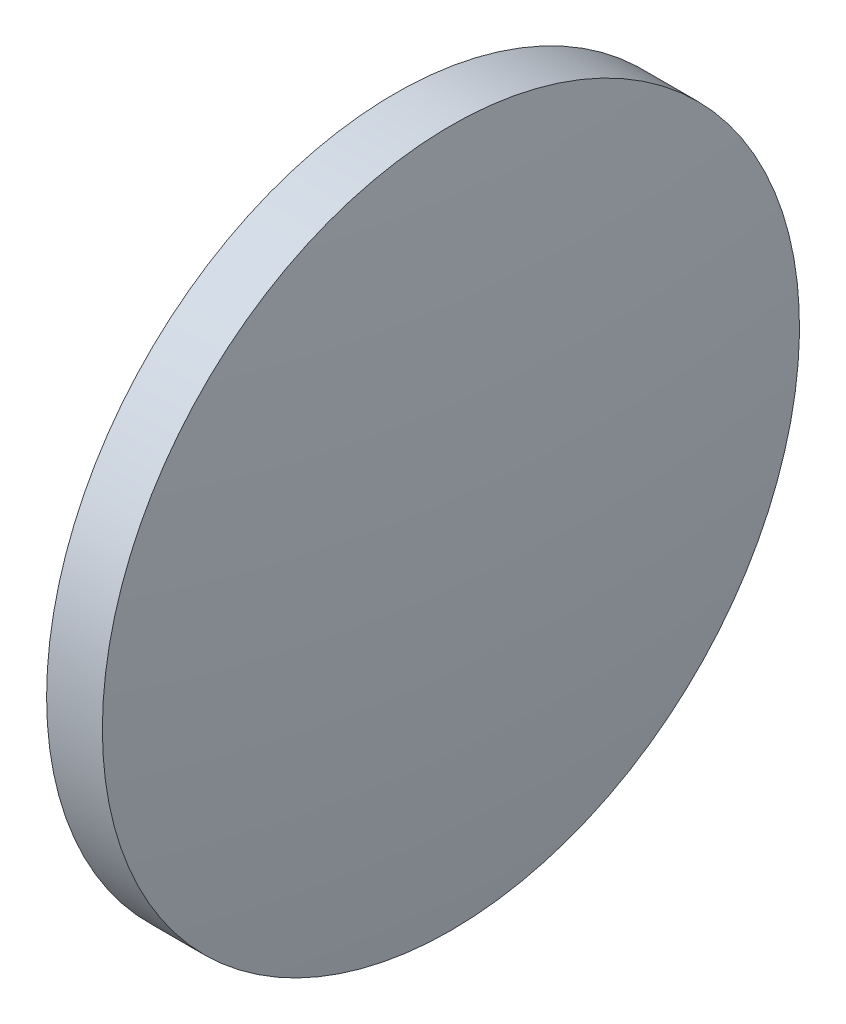
SolidWorks part; units mm, degrees
ref_plane "前视基准面" through (0, 0, 0) normal (0, 0, 1) x (1, 0, 0)
ref_plane "上视基准面" through (0, 0, 0) normal (0, 1, 0) x (1, 0, 0)
ref_plane "右视基准面" through (0, 0, 0) normal (1, 0, 0) x (0, 0, -1)
sketch "草图1" plane through (0, 0, 0) normal (0, 0, 1) x (1, 0, 0)
  line L0 (401.0823, 108.2513) -> (410.6704, 108.2513) construction
  line L1 (403.4479, 108.2513) -> (403.4479, 120.7513)
  line L2 (406.2079, 108.2513) -> (403.4479, 108.2513)
  line L5 (403.4479, 120.7513) -> (405.4479, 120.7513)
  arc A0 (406.2079, 108.2513) -> (405.4479, 120.7513) centre (303.0319, 108.2513) ccw
revolve "旋转1" add sketch "草图1" angle 360 about L0
